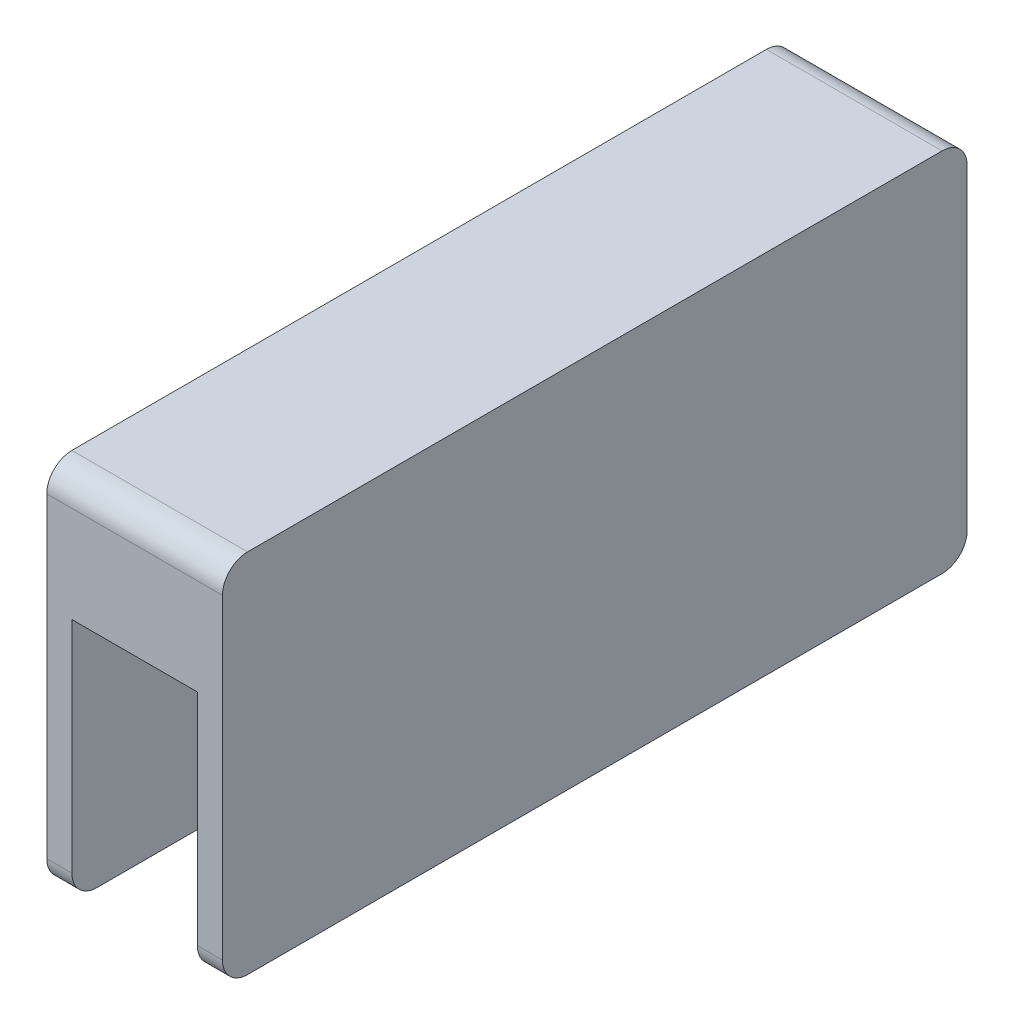
SolidWorks part; units mm, degrees
ref_plane "Plano frontal" through (0, 0, 0) normal (0, 0, 1) x (1, 0, 0)
ref_plane "Plano superior" through (0, 0, 0) normal (0, 1, 0) x (1, 0, 0)
ref_plane "Plano direito" through (0, 0, 0) normal (1, 0, 0) x (0, 0, -1)
sketch "Esboço2" plane through (0, 0, 0) normal (1, 0, 0) x (0, 0, -1)
  line L1 (2.9016, -0.0625) -> (-35.0984, -0.0625) construction
  line L2 (2.9016, -0.0625) -> (-35.0984, -0.0625)
  line L6 (7.6893, -0.0625) -> (2.9016, -0.0625)
  line L8 (-39.8861, -0.0625) -> (-35.0984, -0.0625)
  line L9 (-60.5984, 9.4769) -> (-60.5984, 20.9769)
  line L10 (28.4016, 9.4769) -> (28.4016, 20.9769)
  line L11 (-57.5984, 23.9769) -> (25.4016, 23.9769)
  arc A0 (28.4016, 20.9769) -> (25.4016, 23.9769) centre (25.4016, 20.9769) ccw
  arc A1 (-60.5984, 20.9769) -> (-57.5984, 23.9769) centre (-57.5984, 20.9769) cw
  arc A2 (28.4016, 9.4769) -> (24.5016, 12.3387) centre (25.4016, 9.4769) ccw
  arc A3 (-48.8914, 5.5897) -> (-56.6984, 12.3387) centre (-60.5984, -0.0625) ccw
  arc A4 (-48.8914, 5.5897) -> (-39.8861, -0.0625) centre (-39.8861, 9.9375) ccw
  arc A5 (-60.5984, 9.4769) -> (-56.6984, 12.3387) centre (-57.5984, 9.4769) cw
  arc A6 (16.6946, 5.5897) -> (7.6893, -0.0625) centre (7.6893, 9.9375) cw
  arc A7 (16.6946, 5.5897) -> (24.5016, 12.3387) centre (28.4016, -0.0625) cw
  point P22 (28.4016, 12.9375)
  point P23 (-60.5984, 12.9375)
  dimension "D1" = 3
extrude "Ressalto-extrusão2" add sketch "Esboço2" along normal blind 15
sketch "Esboço3" plane through (0, 0, 0) normal (-1, 0, 0) x (0, 0, 1)
  line L0 (60.5984, 15.2269) -> (60.5984, 20.9769)
  line L1 (60.5984, 20.9769) -> (60.5984, 9.4769) construction
  line L2 (-28.4016, 15.2269) -> (-28.4016, 20.9769)
  line L3 (-28.4016, 9.4769) -> (-28.4016, 20.9769) construction
  line L4 (16.0984, 23.9769) -> (57.5984, 23.9769)
  line L5 (-25.4016, 23.9769) -> (57.5984, 23.9769) construction
  line L6 (16.0984, 23.9769) -> (-25.4016, 23.9769)
  line L7 (60.5984, 15.2269) -> (60.5984, -16.7731)
  line L8 (-28.4016, 15.2269) -> (-28.4016, -16.7731)
  line L9 (57.5984, -19.7731) -> (-25.4016, -19.7731)
  arc A0 (57.5984, 23.9769) -> (60.5984, 20.9769) centre (57.5984, 20.9769) cw
  arc A1 (-28.4016, 20.9769) -> (-25.4016, 23.9769) centre (-25.4016, 20.9769) cw
  arc A2 (-28.4016, -16.7731) -> (-25.4016, -19.7731) centre (-25.4016, -16.7731) ccw
  arc A3 (60.5984, -16.7731) -> (57.5984, -19.7731) centre (57.5984, -16.7731) cw
  dimension "D1" = 3
  dimension "D2" = 3
extrude "Ressalto-extrusão3" add sketch "Esboço3" along normal blind 3
sketch "Esboço4" plane through (15, 0, 0) normal (1, 0, 0) x (0, 0, -1)
  line L0 (-16.0984, 23.9769) -> (25.4016, 23.9769)
  line L1 (25.4016, 23.9769) -> (-57.5984, 23.9769) construction
  line L2 (-16.0984, 23.9769) -> (-57.5984, 23.9769)
  line L3 (28.4016, 15.2269) -> (28.4016, 20.9769)
  line L4 (28.4016, 9.4769) -> (28.4016, 20.9769) construction
  line L5 (-60.5984, 20.9769) -> (-60.5984, 15.2269)
  line L7 (28.4016, 15.2269) -> (28.4016, -16.7731)
  line L8 (28.4016, 9.4769) -> (28.4016, -16.7731) construction
  line L9 (-60.5984, 20.9769) -> (-60.5984, 9.4769) construction
  line L10 (-60.5984, 15.2269) -> (-60.5984, -16.7731)
  line L11 (25.4016, -19.7731) -> (-57.5984, -19.7731)
  arc A0 (25.4016, 23.9769) -> (28.4016, 20.9769) centre (25.4016, 20.9769) cw
  arc A1 (-60.5984, 20.9769) -> (-57.5984, 23.9769) centre (-57.5984, 20.9769) cw
  arc A2 (-60.5984, -16.7731) -> (-57.5984, -19.7731) centre (-57.5984, -16.7731) ccw
  arc A3 (28.4016, -16.7731) -> (25.4016, -19.7731) centre (25.4016, -16.7731) cw
  point P23 (28.4016, -19.7731)
  dimension "D1" = 3
extrude "Ressalto-extrusão4" add sketch "Esboço4" along normal blind 3
